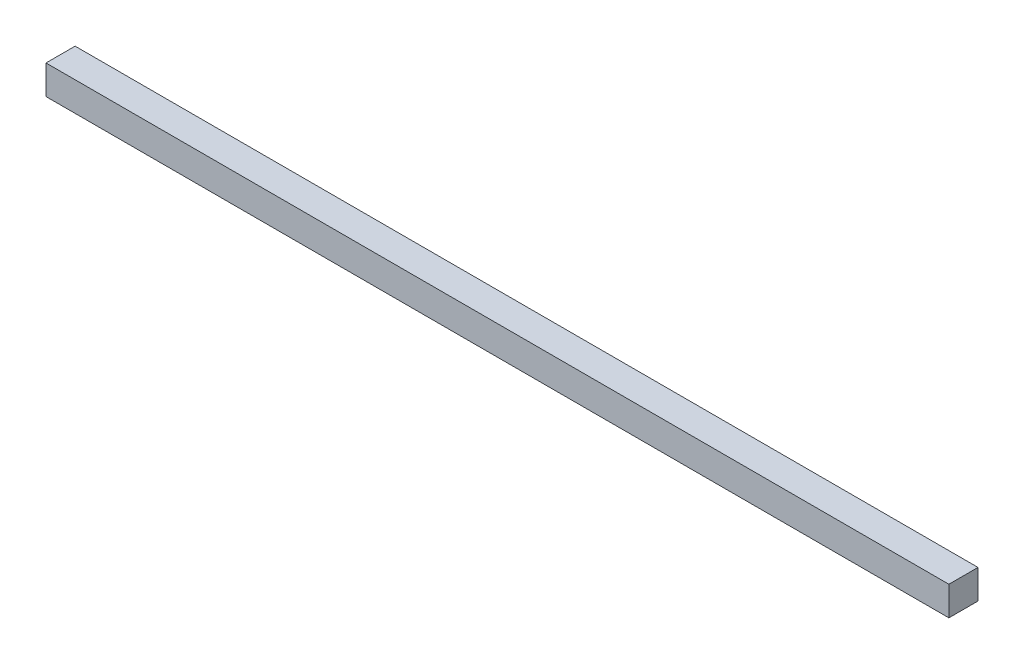
SolidWorks part; units mm, degrees
ref_plane "Front Plane" through (0, 0, 0) normal (0, 0, 1) x (1, 0, 0)
ref_plane "Top Plane" through (0, 0, 0) normal (0, 1, 0) x (1, 0, 0)
ref_plane "Right Plane" through (0, 0, 0) normal (1, 0, 0) x (0, 0, -1)
sketch "Sketch1" plane through (0, 0, 0) normal (0, 1, 0) x (1, 0, 0)
  line L0 (-155, 5) -> (155, -5) construction
  line L1 (-155, 5) -> (155, 5)
  line L2 (-155, 5) -> (-155, -5)
  line L3 (-155, -5) -> (155, -5)
  line L4 (155, 5) -> (155, -5)
  dimension "D1" = 310
  dimension "D2" = 10
extrude "Boss-Extrude1" add sketch "Sketch1" along normal blind 10
